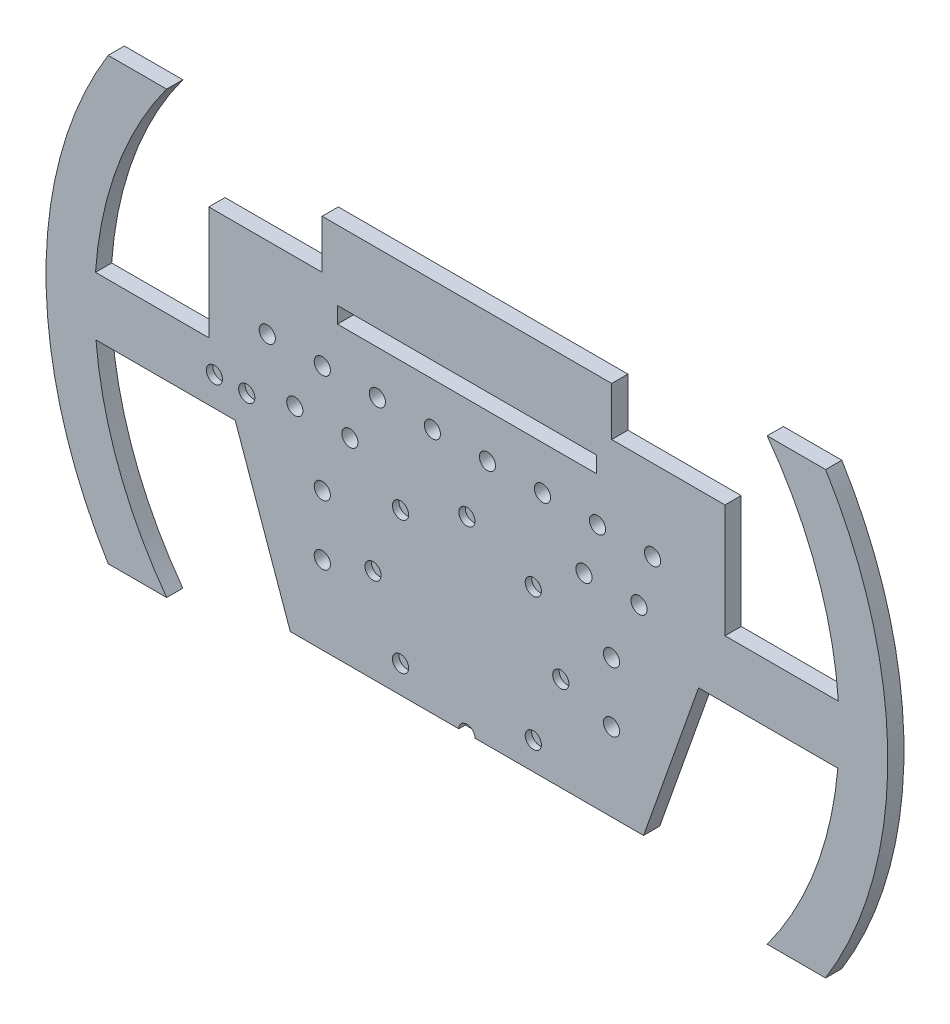
SolidWorks part; units mm, degrees
material "1.6566 (17NiCrMo6-4)"
ref_plane "Plan de face" through (0, 0, 0) normal (0, 0, 1) x (1, 0, 0)
ref_plane "Plan de dessus" through (0, 0, 0) normal (0, 1, 0) x (1, 0, 0)
ref_plane "Plan de droite" through (0, 0, 0) normal (1, 0, 0) x (0, 0, -1)
sketch "Esquisse1" plane through (0, 0, 0) normal (0, 0, 1) x (1, 0, 0)
  line L0 (0, 0) -> (296.2293, 0) construction
  line L1 (0, 0) -> (0, 97.4663) construction
  line L3 (-79.7214, -10) -> (-79.7214, 25)
  line L4 (-79.7214, 25) -> (-44.7214, 25)
  line L5 (-44.7214, 25) -> (-44.7214, 40)
  line L6 (-44.7214, 40) -> (44.7214, 40)
  line L7 (79.7214, -10) -> (114.7214, -10)
  line L8 (79.7214, -10) -> (79.7214, 25)
  line L9 (79.7214, 25) -> (44.7214, 25)
  line L10 (44.7214, 25) -> (44.7214, 40)
  line L11 (0, -18) -> (-148.6579, -18) construction
  line L12 (71.5644, -28) -> (114.5644, -28)
  line L13 (92.7416, -86) -> (110.7971, -86)
  line L20 (92.7416, 50) -> (110.7971, 50)
  line L21 (-54.56, -76) -> (54.56, -76)
  line L22 (54.56, -76) -> (71.5644, -28)
  line L23 (-79.7214, -10) -> (-114.7214, -10)
  line L25 (-54.56, -76) -> (-71.5644, -28)
  line L26 (-71.5644, -28) -> (-114.5644, -28)
  line L27 (-92.7416, 50) -> (-110.7971, 50)
  line L28 (-92.7416, -86) -> (-110.7971, -86)
  arc A1 (110.7971, 50) -> (110.7971, -86) centre (0, -18) cw
  arc A4 (-110.7971, 50) -> (-110.7971, -86) centre (0, -18) ccw
  arc A5 (-92.7416, 50) -> (-92.7416, -86) centre (0, -18) ccw
  arc A7 (92.7416, 50) -> (92.7416, -86) centre (0, -18) cw
  point P21 (0, 40)
  point P29 (0, -76)
  dimension "D2" = 35
  dimension "D11" = 115
  dimension "D14" = 54.56
  dimension "D15" = 43
  dimension "D13" = 130
  dimension "D3" = 8
  dimension "D4" = 35
  dimension "D5" = 15
  dimension "D6" = 48
  dimension "D7" = 35
  dimension "D8" = 18
  dimension "D9" = 10
  dimension "D10" = 10
  dimension "D12" = 10
extrude "Boss.-Extru.1" add sketch "Esquisse1" along normal blind 5 contours A7 L7 L8 L9 L10 L6 L5 L4 L3 L23 A5 L26 L25 L21 L22 L12 | A5 L27 A4 L28 | A7 L13 A1 L20
sketch "Esquisse2" plane through (0, 0, 5) normal (0, 0, 1) x (1, 0, 0)
  line L0 (0, 0) -> (0, 60.033) construction
  line L1 (0, 0) -> (89.5007, 0) construction
  line L2 (-44.7214, 40) -> (44.7214, 40)
  line L3 (-40, 18.5) -> (40, 18.5)
  line L4 (-40, 18.5) -> (-40, 13.5)
  line L5 (-40, 13.5) -> (40, 13.5)
  line L6 (40, 18.5) -> (40, 13.5)
  line L7 (-40, 18.5) -> (40, 13.5) construction
  line L8 (-40, 13.5) -> (40, 18.5) construction
  point P1 (0, 16)
  dimension "D1" = 80
  dimension "D2" = 5
  dimension "D3" = 21.5
extrude "Enlèv. mat.-Extru.1" cut sketch "Esquisse2" against normal blind 10 contours L6 L3 L4 L5
sketch "Esquisse3" plane through (0, 0, 5) normal (0, 0, 1) x (1, 0, 0)
  line L0 (0, 0) -> (0, 59.4514) construction
  line L1 (0, 0) -> (88.4436, 0) construction
  line L6 (-79.7214, -10) -> (-114.7214, -10) construction
  circle A2 centre (-68, -19) radius 2.5
  circle A3 centre (-78, -19) radius 2.5
  point P10 (0, 0)
  point P14 (0, 0)
  point P15 (-68.9361, -19)
  point P16 (0, -9.3023)
  point P17 (0, -30.9136)
  dimension "D7" = 5
  dimension "D8" = 5
  dimension "D3" = 9
  dimension "D4" = 9
  dimension "D5" = 68
  dimension "D6" = 10
extrude "Enlèv. mat.-Extru.6" cut sketch "Esquisse3" against normal blind 2
sketch "Esquisse5" plane through (0, 0, 5) normal (0, 0, 1) x (1, 0, 0)
  line L0 (0, 0) -> (0, 61.7252) construction
  line L1 (0, 0) -> (94.888, 0) construction
  line L2 (0, 0) -> (0, -12)
  circle A2 centre (0, -18) radius 2.5
  circle A3 centre (20.5061, -26.4939) radius 2.5
  circle A4 centre (29, -47) radius 2.5
  circle A5 centre (20.5061, -67.5061) radius 2.5
  circle A6 centre (0, -76) radius 2.5
  circle A7 centre (-20.5061, -67.5061) radius 2.5
  circle A8 centre (-29, -47) radius 2.5
  circle A9 centre (-20.5061, -26.4939) radius 2.5
  point P4 (0, 0)
  point P7 (0, 0)
  point P9 (0, 0)
  point P10 (0, 0)
  point P31 (0, -47)
  dimension "D1" = 12
  dimension "D3" = 5
  dimension "D4" = 8
extrude "Enlèv. mat.-Extru.10" cut sketch "Esquisse5" against normal blind 2
sketch "Esquisse6" plane through (0, 0, 5) normal (0, 0, 1) x (1, 0, 0)
  line L0 (0, 0) -> (0, 72.5257) construction
  line L1 (0, 0) -> (162.0084, 0) construction
  circle A0 centre (-61.6599, 0) radius 2.5
  circle A1 centre (-44.6599, 0) radius 2.5
  circle A2 centre (-27.6599, 0) radius 2.5
  circle A3 centre (-10.6599, 0) radius 2.5
  circle A4 centre (6.3401, 0) radius 2.5
  circle A5 centre (23.3401, 0) radius 2.5
  circle A6 centre (40.3401, 0) radius 2.5
  circle A7 centre (57.3401, 0) radius 2.5
  circle A8 centre (-53.1599, -15.0346) radius 2.5
  circle A9 centre (-36.1599, -15.0346) radius 2.5
  circle A10 centre (-44.6599, -33.3726) radius 2.5
  circle A11 centre (-44.6599, -51.8787) radius 2.5
  circle A12 centre (44.6599, -51.8787) radius 2.5
  circle A13 centre (44.6599, -33.3726) radius 2.5
  circle A14 centre (36.1599, -15.0346) radius 2.5
  circle A15 centre (53.1599, -15.0346) radius 2.5
  dimension "D1" = 8.5
  dimension "D3" = 5
  dimension "D4" = 5
  dimension "D5" = 5
  dimension "D6" = 5
  dimension "D7" = 17
  dimension "D2" = 17
  dimension "D8" = 17
extrude "Enlèv. mat.-Extru.12" cut sketch "Esquisse6" against normal through all
